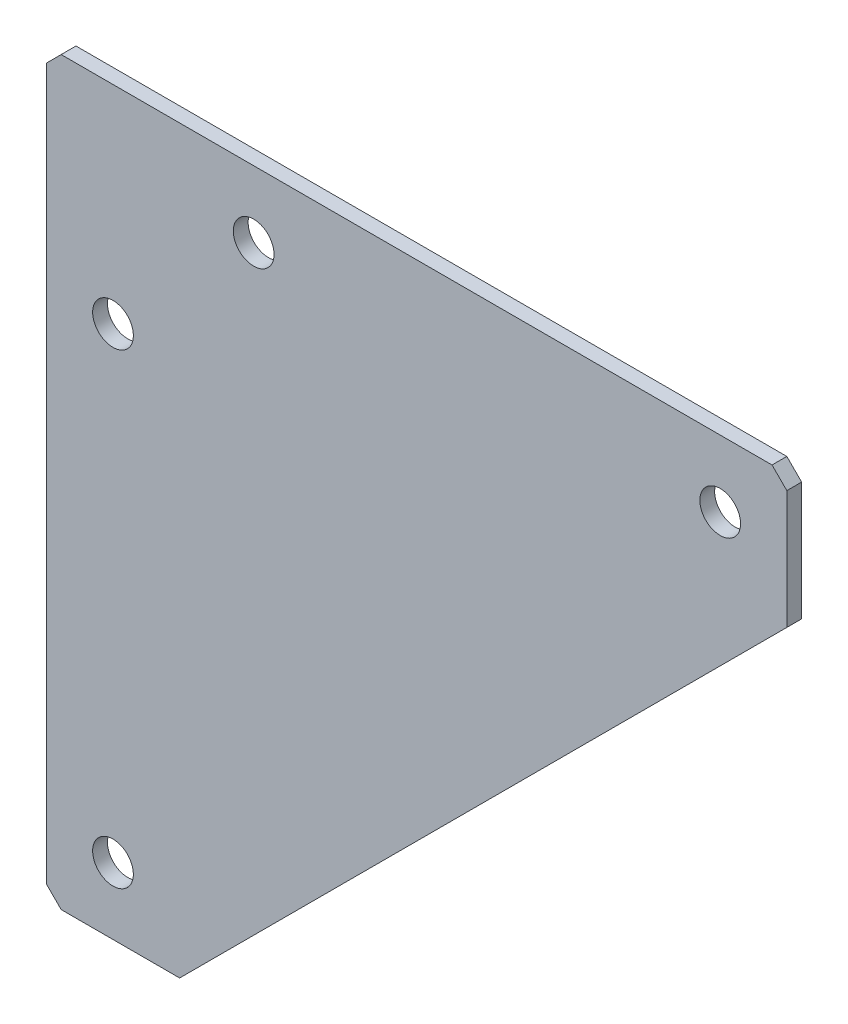
SolidWorks part; units mm, degrees
ref_plane "Front Plane" through (0, 0, 0) normal (0, 0, 1) x (1, 0, 0)
ref_plane "Top Plane" through (0, 0, 0) normal (0, 1, 0) x (1, 0, 0)
ref_plane "Right Plane" through (0, 0, 0) normal (1, 0, 0) x (0, 0, -1)
ref_plane "Plane1" through (0, 0, 0) normal (0, 0, 1) x (1, 0, 0)
sketch "Sketch1" plane through (0, 0, 0) normal (0, 0, 1) x (1, 0, 0)
  line L0 (0, 98) -> (0, 2)
  line L1 (0, 2) -> (2, 0)
  line L2 (2, 0) -> (18, 0)
  line L3 (18, 0) -> (100, 82)
  line L4 (100, 82) -> (100, 98)
  line L5 (100, 98) -> (98, 100)
  line L6 (98, 100) -> (2, 100)
  line L7 (2, 100) -> (0, 98)
  circle A0 centre (91, 91) radius 2.75
  circle A1 centre (28, 91) radius 2.75
  circle A2 centre (9, 9) radius 2.75
  circle A3 centre (9, 72) radius 2.75
extrude "Boss-Extrude1" add sketch "Sketch1" against normal blind 2
